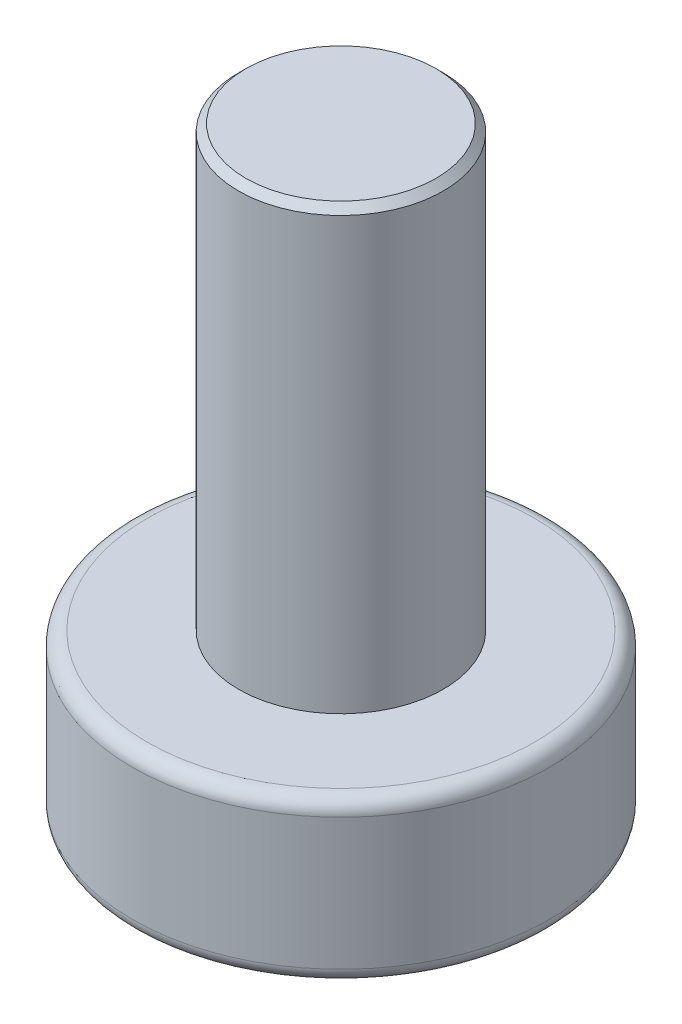
SolidWorks part; units mm, degrees
ref_plane "Спереди" through (0, 0, 0) normal (0, 0, 1) x (1, 0, 0)
ref_plane "Сверху" through (0, 0, 0) normal (0, 1, 0) x (1, 0, 0)
ref_plane "Справа" through (0, 0, 0) normal (1, 0, 0) x (0, 0, -1)
sketch "Эскиз1" plane through (0, 0, 0) normal (0, 1, 0) x (1, 0, 0)
  circle A0 centre (0, 0) radius 2.85
  dimension "D1" = 5.7
extrude "Бобышка-Вытянуть1" add sketch "Эскиз1" along normal blind 2.2
sketch "Эскиз2" plane through (0, 2.2, 0) normal (0, 1, 0) x (1, 0, 0)
  circle A0 centre (0, 0) radius 1.4
  dimension "D1" = 2.8
extrude "Бобышка-Вытянуть2" add sketch "Эскиз2" along normal blind 6
chamfer "Фаска1" distance 0.1 angle 45 1 edges at (0, 8.2, 1.4)
fillet "Скругление1" radius 0.2 2 edges at (0, 2.2, 2.85) (0, 0, 2.85)
sketch "Эскиз3" plane through (0, 0, 0) normal (0, -1, 0) x (1, 0, 0)
  line L0 (-0.5, 0.5) -> (-0.5, 2)
  line L1 (-0.5, 2) -> (0.5, 2)
  line L2 (0.5, 2) -> (0.5, 0.5)
  line L3 (0.5, 0.5) -> (2, 0.5)
  line L4 (2, 0.5) -> (2, -0.5)
  line L5 (2, -0.5) -> (0.5, -0.5)
  line L6 (0.5, -0.5) -> (0.5, -2)
  line L7 (0.5, -2) -> (-0.5, -2)
  line L8 (-0.5, -2) -> (-0.5, -0.5)
  line L9 (-0.5, -0.5) -> (-2, -0.5)
  line L10 (-2, -0.5) -> (-2, 0.5)
  line L11 (-2, 0.5) -> (-0.5, 0.5)
  point P12 (0, 2)
  point P13 (0, -2)
  point P15 (-2, 0)
  point P16 (2, 0)
  dimension "D1" = 4
  dimension "D2" = 1
extrude "Вырез-Вытянуть1" cut sketch "Эскиз3" against normal blind 1.5
